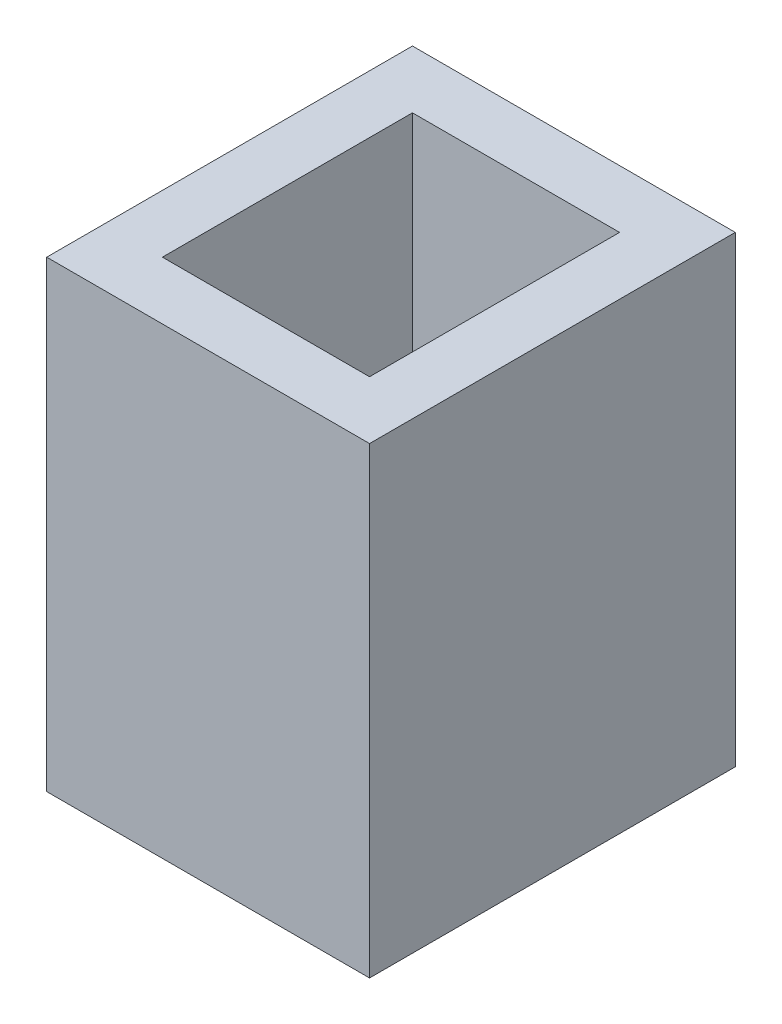
SolidWorks part; units mm, degrees
ref_plane "Front Plane" through (0, 0, 0) normal (0, 0, 1) x (1, 0, 0)
ref_plane "Top Plane" through (0, 0, 0) normal (0, 1, 0) x (1, 0, 0)
ref_plane "Right Plane" through (0, 0, 0) normal (1, 0, 0) x (0, 0, -1)
sketch "Sketch1" plane through (0, 0, 0) normal (0, 1, 0) x (1, 0, 0)
  line L1 (-8.8582, -10.0355) -> (8.8582, -10.0355)
  line L2 (-8.8582, -10.0355) -> (-8.8582, 10.0355)
  line L3 (-8.8582, 10.0355) -> (8.8582, 10.0355)
  line L4 (8.8582, -10.0355) -> (8.8582, 10.0355)
  line L5 (0, 10.0355) -> (0, -10.0355) construction
  line L6 (-8.8582, 0) -> (8.8582, 0) construction
  line L7 (-5.6833, -6.8605) -> (5.6833, -6.8605)
  line L8 (-5.6833, -6.8605) -> (-5.6833, 6.8605)
  line L9 (-5.6833, 6.8605) -> (5.6833, 6.8605)
  line L10 (5.6833, -6.8605) -> (5.6833, 6.8605)
  line L11 (0, 6.8605) -> (0, -6.8605) construction
  line L12 (-5.6833, 0) -> (5.6833, 0) construction
  point P0 (0, 0)
  point P4 (0, 0)
  dimension "D1" = 13.7211
  dimension "D2" = 11.3665
  dimension "D3" = 3.175
  dimension "D4" = 3.175
extrude "Boss-Extrude1" add sketch "Sketch1" along normal blind 25.4
